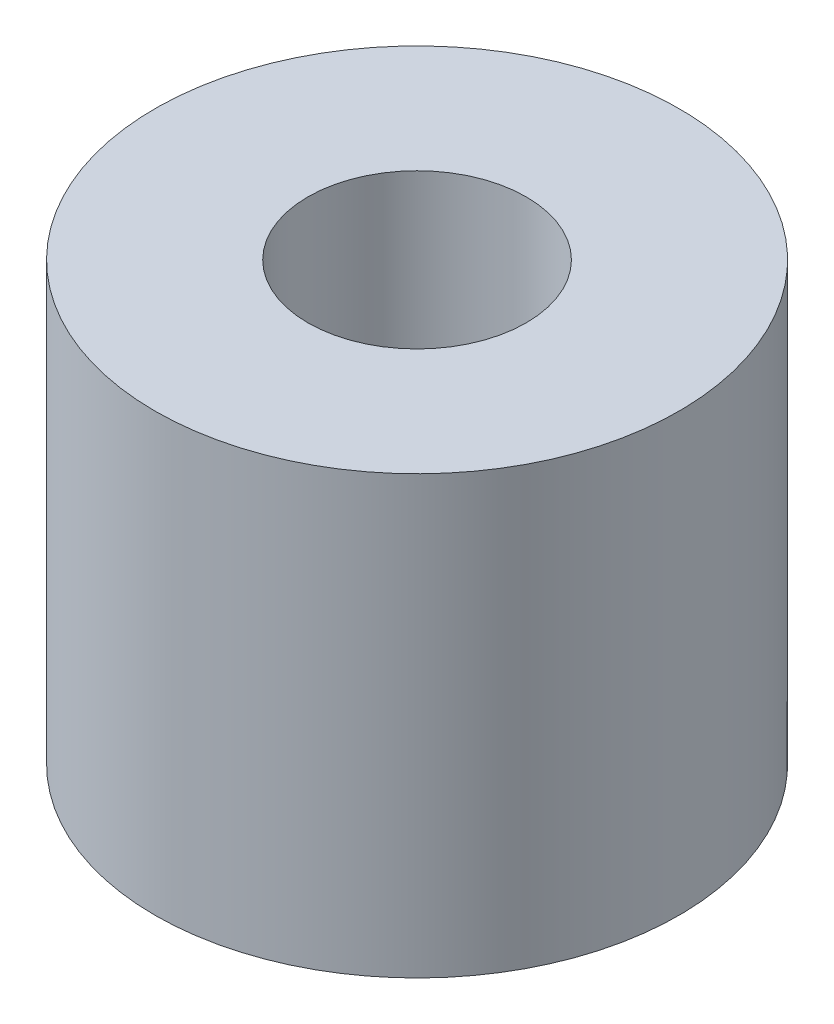
SolidWorks part; units mm, degrees
ref_plane "Front Plane" through (0, 0, 0) normal (0, 0, 1) x (1, 0, 0)
ref_plane "Top Plane" through (0, 0, 0) normal (0, 1, 0) x (1, 0, 0)
ref_plane "Right Plane" through (0, 0, 0) normal (1, 0, 0) x (0, 0, -1)
sketch "Sketch1" plane through (0, 0, 0) normal (0, 1, 0) x (1, 0, 0)
  circle A0 centre (0, 0) radius 1.5875
  circle A1 centre (0, 0) radius 3.81
  dimension "D1" = 3.175
  dimension "D2" = 7.62
extrude "Boss-Extrude1" add sketch "Sketch1" along normal blind 6.35
